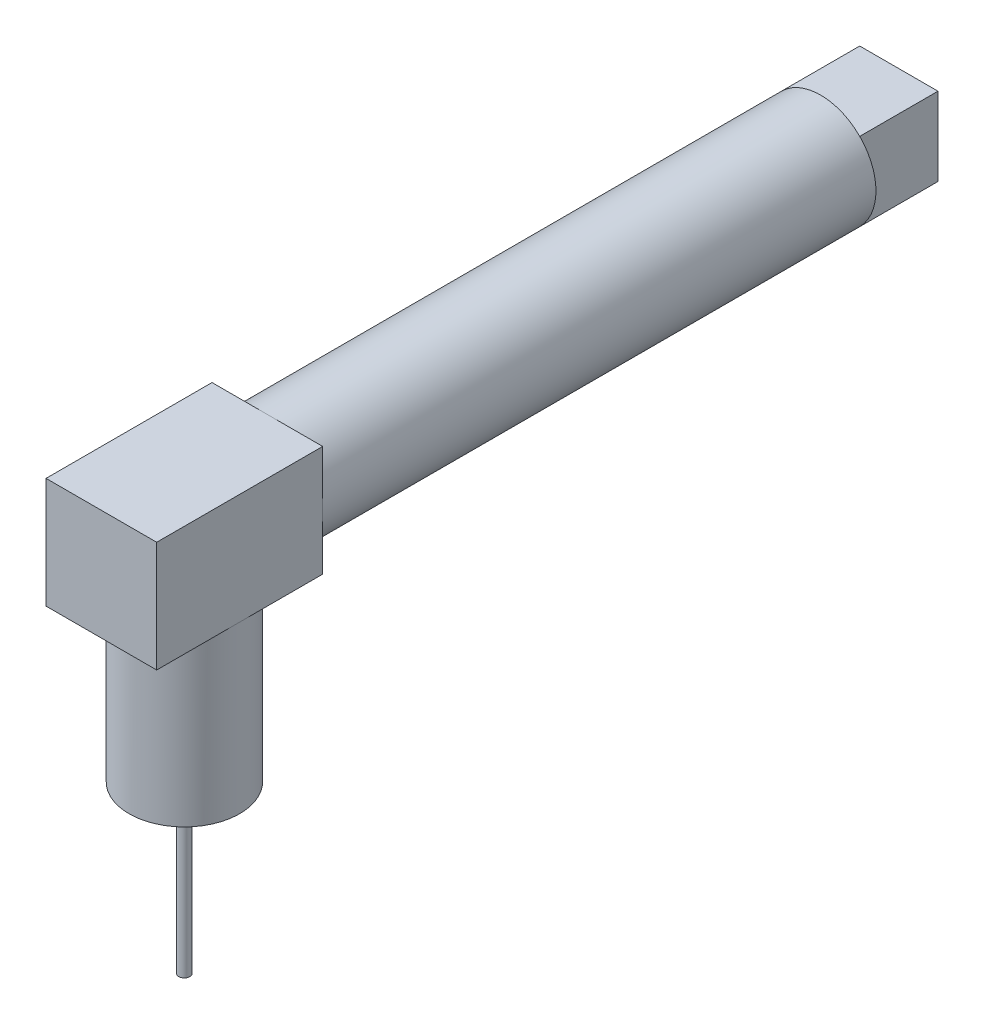
SolidWorks part; units mm, degrees
ref_plane "Alzado" through (0, 0, 0) normal (0, 0, 1) x (1, 0, 0)
ref_plane "Planta" through (0, 0, 0) normal (0, 1, 0) x (1, 0, 0)
ref_plane "Vista lateral" through (0, 0, 0) normal (1, 0, 0) x (0, 0, -1)
sketch "Croquis2" plane through (0, 0, 0) normal (0, 0, 1) x (1, 0, 0)
  circle A0 centre (0, 0) radius 5
extrude "Saliente-Extruir1" add sketch "Croquis2" along normal blind 50
sketch "Croquis3" plane through (0, 0, 50) normal (0, 0, 1) x (1, 0, 0)
  line L1 (-5, -5) -> (5, -5)
  line L2 (-5, -5) -> (-5, 5)
  line L3 (-5, 5) -> (5, 5)
  line L4 (5, -5) -> (5, 5)
  line L5 (-5, -5) -> (5, 5) construction
  line L6 (-5, 5) -> (5, -5) construction
  circle A0 centre (0, 0) radius 5 construction
  point P0 (0, 0)
  point P6 (0, 0)
extrude "Saliente-Extruir2" add sketch "Croquis3" along normal blind 15
sketch "Croquis5" plane through (0, -5, 0) normal (0, -1, 0) x (1, 0, 0)
  line L0 (-5, 65) -> (5, 65) construction
  line L1 (-5, 65) -> (-5, 50) construction
  circle A0 centre (0, 57.5) radius 5
  point P4 (0, 0)
  dimension "D1" = 7.5
  dimension "D2" = 5
extrude "Saliente-Extruir3" add sketch "Croquis5" along normal blind 15
sketch "Croquis8" plane through (0, -20, 0) normal (0, -1, 0) x (1, 0, 0)
  circle A0 centre (0, 57.5) radius 0.5
extrude "Saliente-Extruir4" add sketch "Croquis8" along normal blind 15
sketch "Croquis11" plane through (0, 0, 0) normal (0, 0, -1) x (-1, 0, 0)
  line L1 (-3.5355, -3.5355) -> (3.5355, -3.5355)
  line L2 (-3.5355, -3.5355) -> (-3.5355, 3.5355)
  line L3 (-3.5355, 3.5355) -> (3.5355, 3.5355)
  line L4 (3.5355, -3.5355) -> (3.5355, 3.5355)
  line L5 (-3.5355, -3.5355) -> (3.5355, 3.5355) construction
  line L6 (-3.5355, 3.5355) -> (3.5355, -3.5355) construction
  arc A0 (5, 0) -> (0, 5) centre (0, 0) ccw construction
  point P0 (0, 0)
  point P9 (0, 0)
  point P10 (-3.5355, 3.5355)
extrude "Saliente-Extruir5" add sketch "Croquis11" along normal blind 7.07
